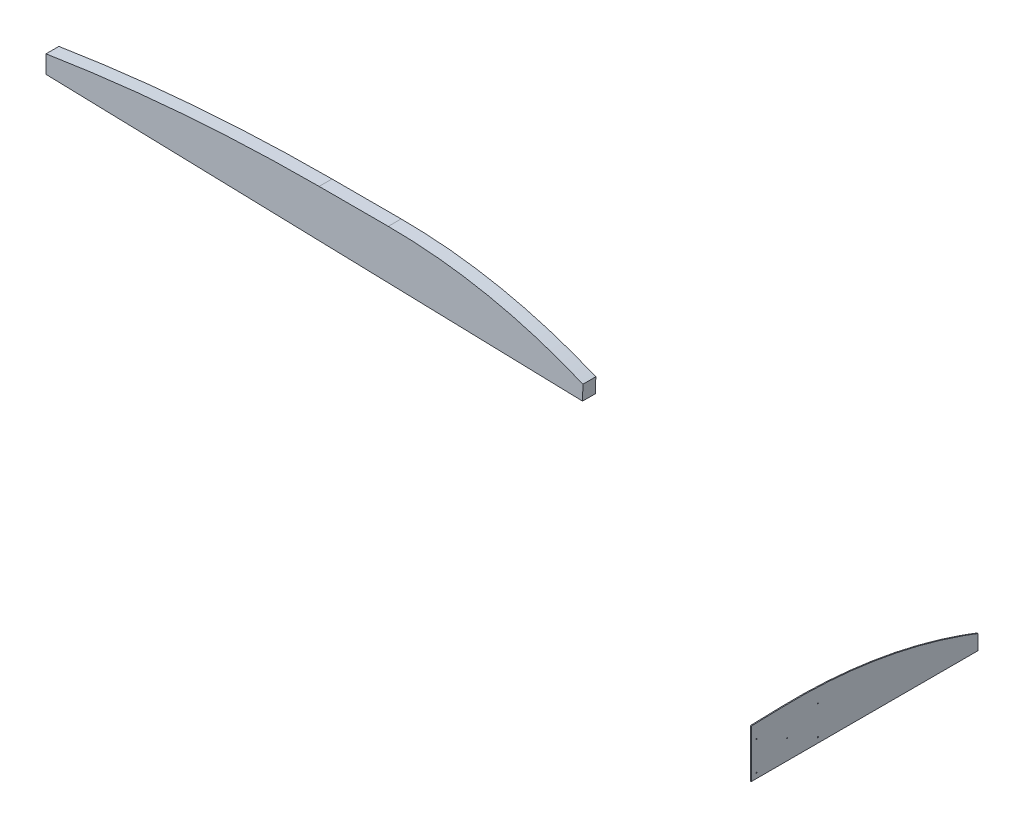
SolidWorks part; units mm, degrees
ref_plane "Front Plane" through (0, 0, 0) normal (0, 0, 1) x (1, 0, 0)
ref_plane "Top Plane" through (0, 0, 0) normal (0, 1, 0) x (1, 0, 0)
ref_plane "Right Plane" through (0, 0, 0) normal (1, 0, 0) x (0, 0, -1)
sketch "Sketch1" plane through (0, 0, 0) normal (0, 0, 1) x (1, 0, 0)
  line L0 (-6816.5014, 2688.9172) -> (-1527.2143, 2543.4856) construction
  line L1 (-1523.1804, 2690.1974) -> (-1527.2143, 2543.4856) construction
  line L2 (-4124.1014, 3078.5028) -> (-3442.1014, 3078.5028) construction
  line L3 (-6816.5014, 2864.3082) -> (-6816.5014, 2684.7269) construction
  line L4 (-6816.5014, 2688.9172) -> (-1527.2143, 2543.4856)
  line L5 (-1523.1804, 2690.1974) -> (-1527.2143, 2543.4856)
  line L6 (-4124.1014, 3078.5028) -> (-3442.1014, 3078.5028)
  line L7 (-6816.5014, 2864.3082) -> (-6816.5014, 2684.7269)
  arc A0 (-1523.1804, 2690.1974) -> (-3442.1014, 3078.5028) centre (-3442.1014, -1857.0964) ccw construction
  arc A1 (-4124.1014, 3078.5028) -> (-6816.5014, 2864.3082) centre (-4124.1014, -13950.1652) ccw construction
  arc A2 (-1523.1804, 2690.1974) -> (-3442.1014, 3078.5028) centre (-3442.1014, -1857.0964) ccw
  arc A3 (-4124.1014, 3078.5028) -> (-6816.5014, 2864.3082) centre (-4124.1014, -13950.1652) ccw
extrude "Boss-Extrude1" add sketch "Sketch1" along normal blind 127 contours L6 A3 L7 L4 L5 A2
sketch "Sketch2" plane through (0, 0, 0) normal (1, 0, 0) x (0, 0, -1)
  line L0 (0.0047, 473.7597) -> (306.336, 482.1825)
  line L1 (2235.2047, 146.7656) -> (2235.2047, -0.0017)
  line L2 (2082.8, 203.3257) -> (2082.8, 167.188)
  line L3 (0.0047, 473.7597) -> (0.0047, -0.0017)
  line L4 (0.0047, -0.0017) -> (2235.2047, -0.0017)
  line L5 (2083.054, 203.2361) -> (2083.054, 167.188)
  line L6 (2082.8, 167.188) -> (2083.054, 167.188)
  line L7 (2083.054, 203.3257) -> (2083.054, 167.188) construction
  arc A0 (2235.2047, 146.7656) -> (2083.054, 203.2361) centre (441.9916, -4451.5521) ccw
  circle A1 centre (656.357, 337.9336) radius 4.7625
  circle A2 centre (656.357, 50.8) radius 4.7625
  circle A3 centre (50.8, 50.8) radius 4.7625
  circle A4 centre (50.8, 337.9336) radius 4.7625
  circle A5 centre (353.5785, 194.3668) radius 4.7625
  arc A6 (2082.8, 203.3257) -> (306.336, 482.1825) centre (441.9916, -4451.5521) ccw
  text T0 "F" font "TXT" height 12.7
  dimension "D1" = 2235.2
  dimension "D2" = 0.254
extrude "Boss-Extrude2" add sketch "Sketch2" along normal blind 9.398 separate body
